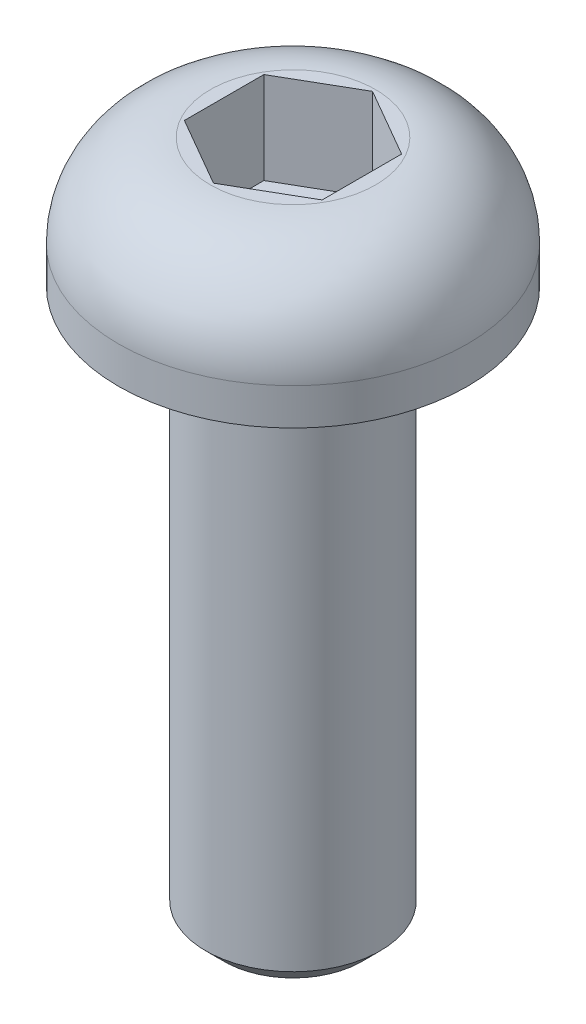
SolidWorks part; units mm, degrees
material "铸造合金钢"
ref_plane "前视基准面" through (0, 0, 0) normal (0, 0, 1) x (1, 0, 0)
ref_plane "上视基准面" through (0, 0, 0) normal (0, 1, 0) x (1, 0, 0)
ref_plane "右视基准面" through (0, 0, 0) normal (1, 0, 0) x (0, 0, -1)
sketch "草图1" plane through (0, 0, 0) normal (0, 1, 0) x (1, 0, 0)
  circle A0 centre (0, 0) radius 1.9
  dimension "D1" = 3.8
extrude "凸台-拉伸1" add sketch "草图1" along normal blind 1.4
sketch "草图2" plane through (0, 1.4, 0) normal (0, 1, 0) x (1, 0, 0)
  line L1 (0, -0.866) -> (0.75, -0.433)
  line L2 (0.75, -0.433) -> (0.75, 0.433)
  line L3 (0.75, 0.433) -> (0, 0.866)
  line L4 (0, 0.866) -> (-0.75, 0.433)
  line L5 (-0.75, 0.433) -> (-0.75, -0.433)
  line L6 (-0.75, -0.433) -> (0, -0.866)
  circle A0 centre (0, 0) radius 0.75 construction
  dimension "D1" = 1.5
extrude "切除-拉伸1" cut sketch "草图2" against normal blind 1
fillet "圆角1" radius 1 1 edges at (0, 1.4, 1.9)
sketch "草图3" plane through (0, 0, 0) normal (0, -1, 0) x (1, 0, 0)
  circle A0 centre (0, 0) radius 0.95
  dimension "D1" = 1.9
extrude "凸台-拉伸2" add sketch "草图3" along normal blind 6
chamfer "倒角1" distance 0.2 angle 45 1 edges at (0, -6, -0.95)
